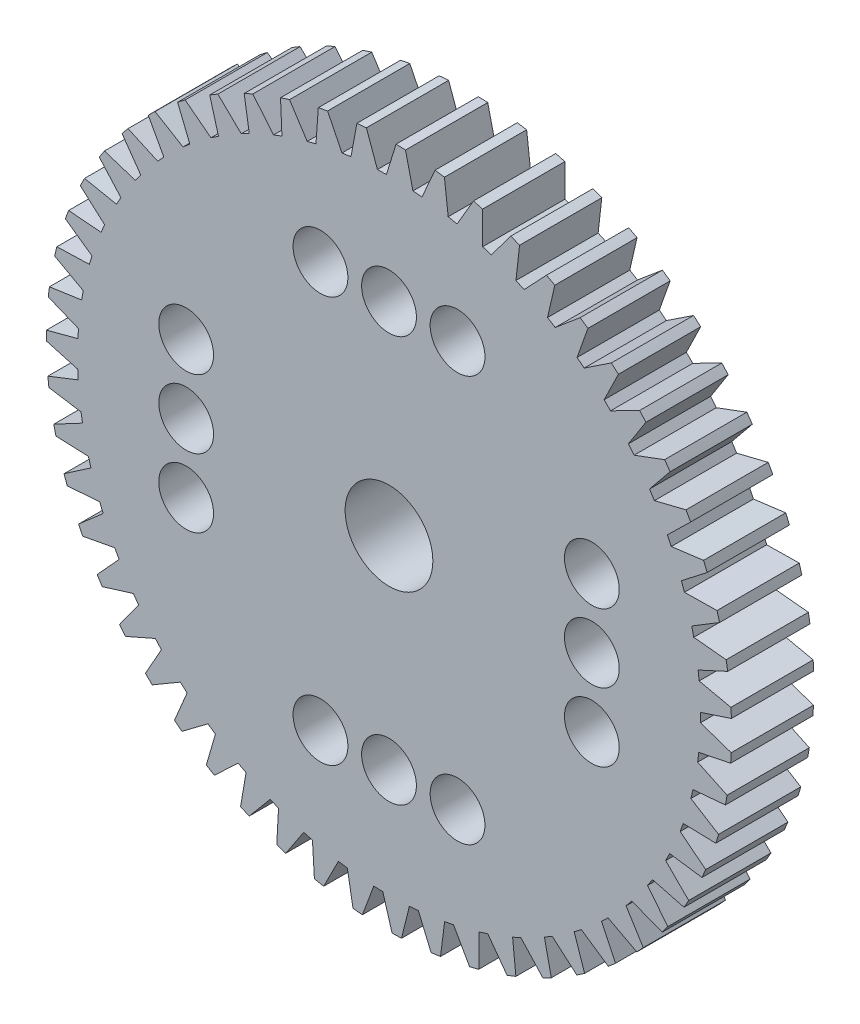
SolidWorks part; units mm, degrees
other "Markup1"
sketch "Sketch3" plane through (-11.5, 11.4999, 3) normal (-0.0441, 0.0247, 0.9987) x (0.9973, -0.0583, 0.0455)
ref_plane "Front Plane" through (0, 0, 0) normal (0, 0, 1) x (1, 0, 0)
ref_plane "Top Plane" through (0, 0, 0) normal (0, 1, 0) x (1, 0, 0)
ref_plane "Right Plane" through (0, 0, 0) normal (1, 0, 0) x (0, 0, -1)
sketch "Sketch1" plane through (0, 0, 0) normal (0, 0, 1) x (1, 0, 0)
  line L2 (-2.5, 7.4) -> (2.5, 7.4) construction
  line L3 (-2.5, -7.4) -> (2.5, -7.4) construction
  line L4 (-7.4, -2.5) -> (-7.4, 2.5) construction
  line L5 (7.4, -2.5) -> (7.4, 2.5) construction
  circle A0 centre (0, 0) radius 12.5
  circle A1 centre (0, 0) radius 10.5 construction
  circle A2 centre (0, 0) radius 1.6
  circle A3 centre (-2.5, 7.4) radius 1
  circle A4 centre (0, 7.4) radius 1
  circle A5 centre (2.5, 7.4) radius 1
  circle A6 centre (2.5, -7.4) radius 1
  circle A7 centre (0, -7.4) radius 1
  circle A8 centre (-2.5, -7.4) radius 1
  circle A9 centre (7.4, -2.5) radius 1
  circle A10 centre (7.4, 0) radius 1
  circle A11 centre (7.4, 2.5) radius 1
  circle A12 centre (-7.4, 2.5) radius 1
  circle A13 centre (-7.4, 0) radius 1
  circle A14 centre (-7.4, -2.5) radius 1
  dimension "D1" = 25
  dimension "D2" = 21
  dimension "D3" = 3.2
  dimension "D4" = 2
  dimension "D5" = 2
  dimension "D6" = 2
  dimension "D10" = 2
  dimension "D11" = 2
  dimension "D12" = 2
  dimension "D7" = 2.5
  dimension "D8" = 2.5
  dimension "D9" = 7.4
  dimension "D13" = 2.5
  dimension "D14" = 2.5
  dimension "D15" = 7.4
extrude "Boss-Extrude1" add sketch "Sketch1" along normal blind 3
sketch "Sketch2" plane through (0, 0, 3) normal (0, 0, 1) x (1, 0, 0)
  line L0 (-6.5438, 10.6642) -> (-7.4471, 10.0542)
  line L1 (-7.4471, 10.0542) -> (-6.4952, 9.3236)
  line L2 (-6.4952, 9.3236) -> (-6.2217, 9.5083)
  line L3 (-6.2217, 9.5083) -> (-6.5438, 10.6642)
  line L4 (-6.4952, 9.3236) -> (-7.5228, 8.6296) construction
  line L5 (-7.5228, 8.6296) -> (-7.8449, 9.7856) construction
  line L6 (-7.8449, 9.7856) -> (-7.4471, 10.0542) construction
  circle A0 centre (0, 0) radius 11.9362 construction
  circle A1 centre (0, 0) radius 12.5 construction
  point P11 (-6.3827, 10.0863)
  point P12 (-6.9711, 9.6889)
  dimension "D1" = 1.09
  dimension "D2" = 0.33
  dimension "D3" = 1.2
  dimension "D4" = 1.2
  dimension "D5" = 1.24
  dimension "D6" = 0.48
  dimension "D7" = 1.2
extrude "Cut-Extrude1" cut sketch "Sketch2" against normal blind 3
pattern_circular "CirPattern1" count 55 over 360 about axis through (0, 0, 0) along (0, 0, 1) of "Cut-Extrude1"
